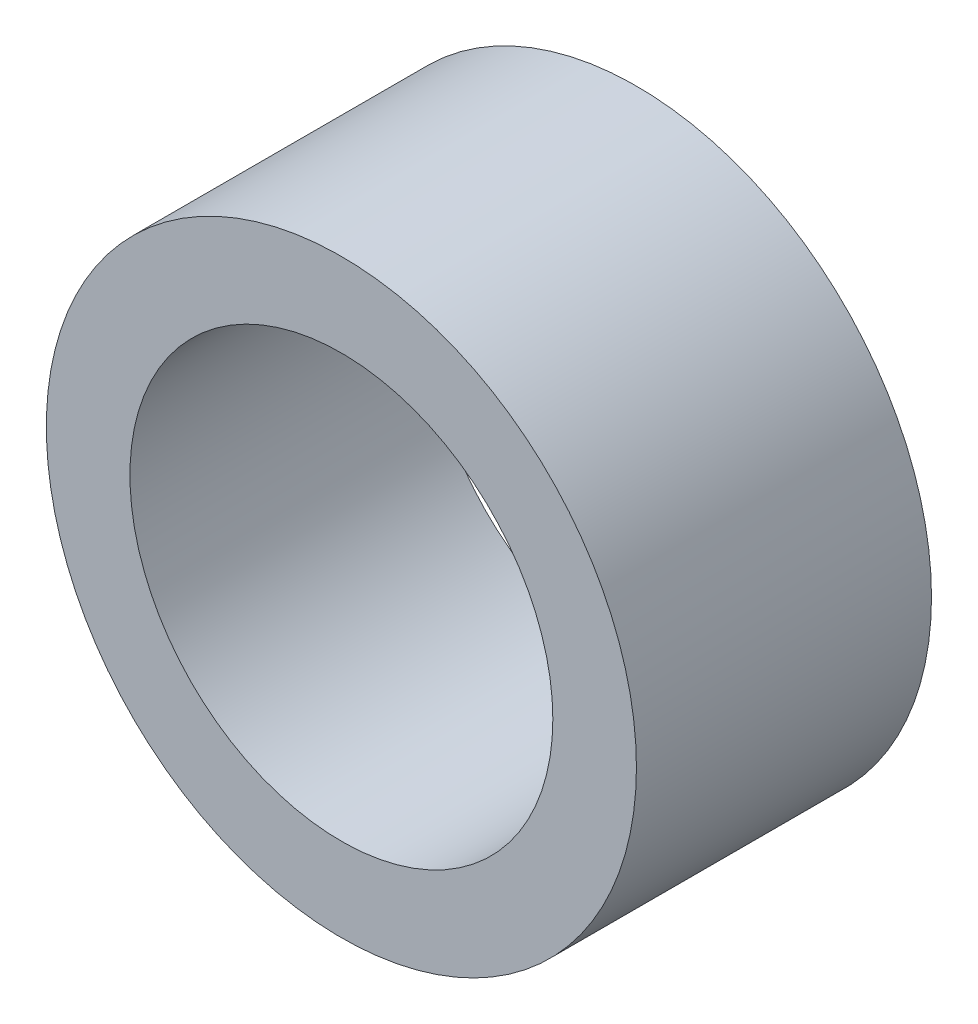
SolidWorks part; units mm, degrees
ref_plane "Front Plane" through (0, 0, 0) normal (0, 0, 1) x (1, 0, 0)
ref_plane "Top Plane" through (0, 0, 0) normal (0, 1, 0) x (1, 0, 0)
ref_plane "Right Plane" through (0, 0, 0) normal (1, 0, 0) x (0, 0, -1)
sketch "Sketch1" plane through (0, 0, 0) normal (0, 0, 1) x (1, 0, 0)
  circle A0 centre (0, 0) radius 2.15
  circle A1 centre (0, 0) radius 3
  dimension "D1" = 4.3
  dimension "D2" = 6
extrude "Boss-Extrude1" add sketch "Sketch1" along normal blind 3
